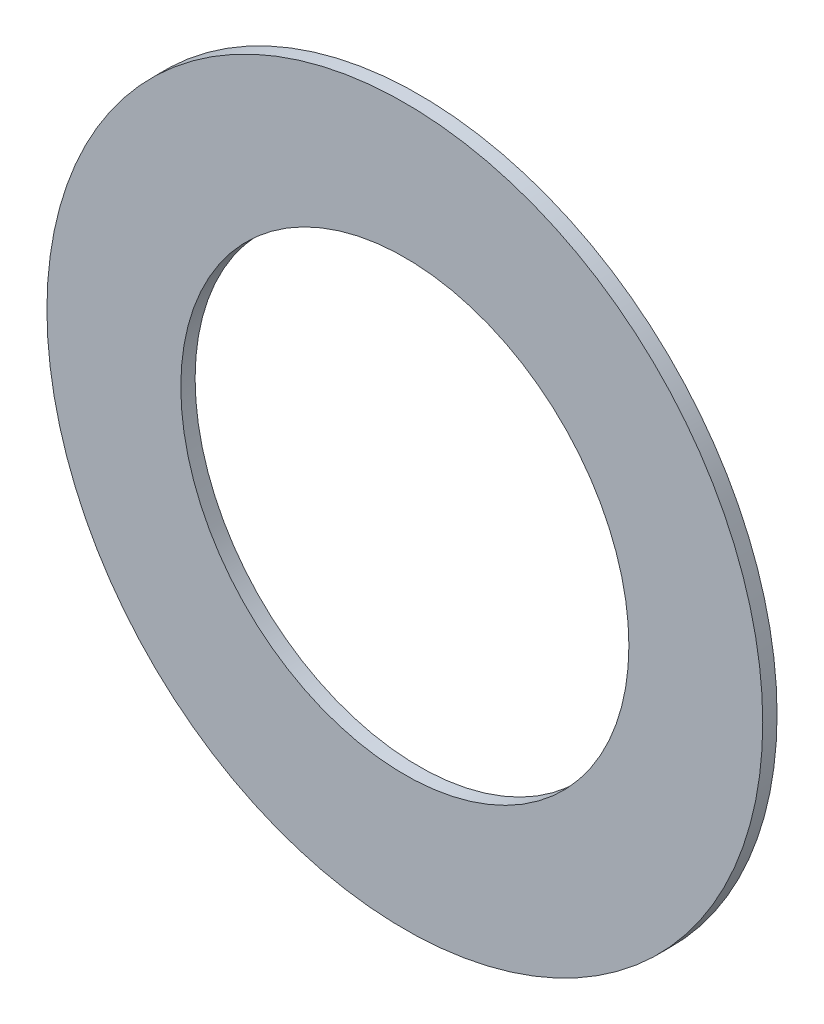
SolidWorks part; units mm, degrees
material "AISI 316 Stainless Steel Sheet (SS)"
ref_plane "Front Plane" through (0, 0, 0) normal (0, 0, 1) x (1, 0, 0)
ref_plane "Top Plane" through (0, 0, 0) normal (0, 1, 0) x (1, 0, 0)
ref_plane "Right Plane" through (0, 0, 0) normal (1, 0, 0) x (0, 0, -1)
sketch "Sketch1" plane through (0, 0, 0) normal (0, 0, 1) x (1, 0, 0)
  circle A0 centre (0, 0) radius 3.9751
  circle A1 centre (0, 0) radius 6.35
  dimension "D1" = 7.9502
  dimension "D2" = 12.7
extrude "Boss-Extrude1" add sketch "Sketch1" along normal blind 0.254
